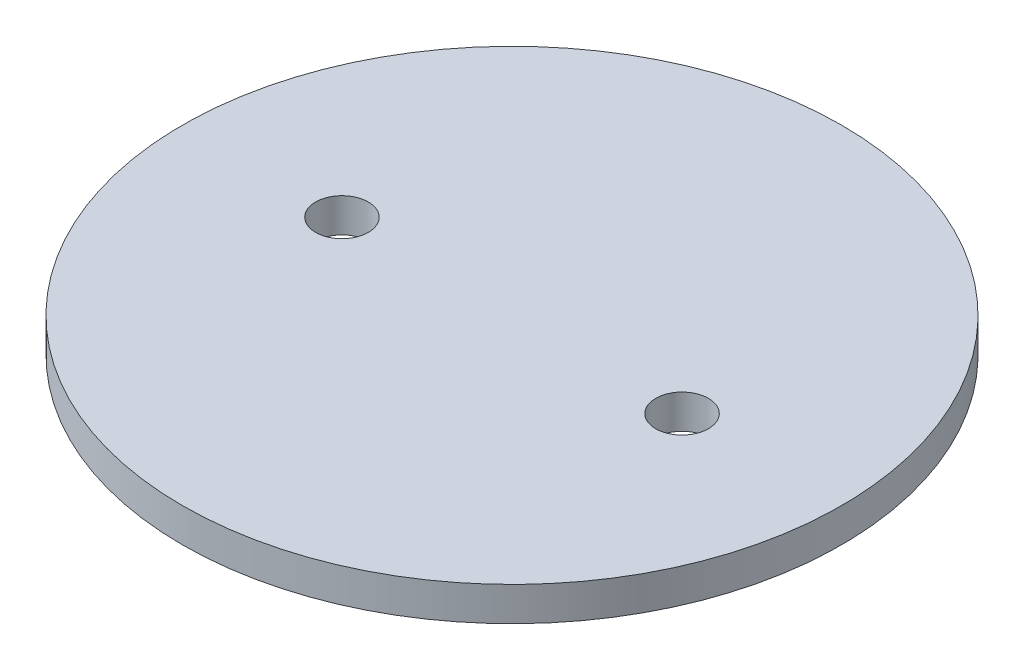
SolidWorks part; units mm, degrees
ref_plane "Front Plane" through (0, 0, 0) normal (0, 0, 1) x (1, 0, 0)
ref_plane "Top Plane" through (0, 0, 0) normal (0, 1, 0) x (1, 0, 0)
ref_plane "Right Plane" through (0, 0, 0) normal (1, 0, 0) x (0, 0, -1)
sketch "Sketch1" plane through (0, 0, 0) normal (0, 1, 0) x (1, 0, 0)
  line L0 (-50, 0) -> (0, 0) construction
  line L1 (0, 0) -> (0, 43.6297) construction
  circle A0 centre (0, 0) radius 96.9
  circle A1 centre (50, 0) radius 7.75
  circle A2 centre (-50, 0) radius 7.75
  dimension "D1" = 193.8
  dimension "D2" = 15.5
  dimension "D3" = 100
extrude "Boss-Extrude1" add sketch "Sketch1" along normal blind 10
